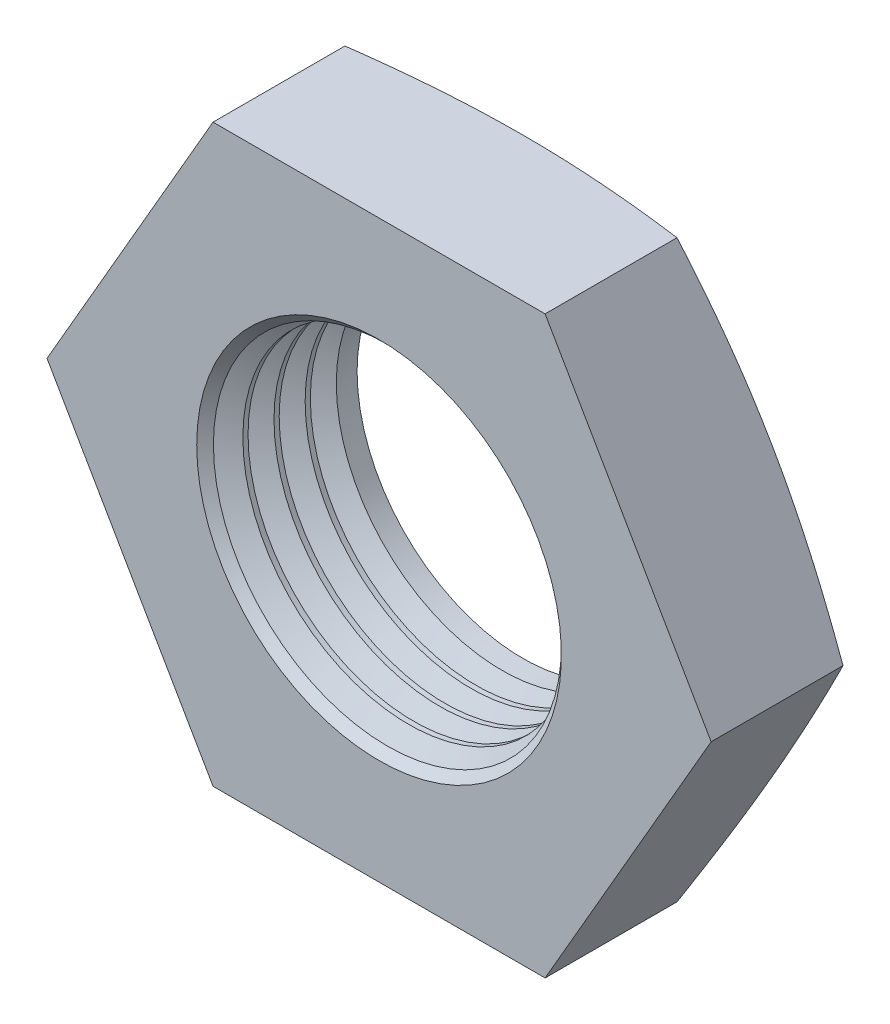
SolidWorks part; units mm, degrees
ref_plane "Front" through (0, 0, 0) normal (0, 0, 1) x (1, 0, 0)
ref_plane "Top" through (0, 0, 0) normal (0, 1, 0) x (1, 0, 0)
ref_plane "Right" through (0, 0, 0) normal (1, 0, 0) x (0, 0, -1)
sketch "Sketch1" plane through (0, 0, 0) normal (0, 0, 1) x (1, 0, 0)
  line L1 (3.4641, -6) -> (6.9282, 0)
  line L2 (6.9282, 0) -> (3.4641, 6)
  line L3 (3.4641, 6) -> (-3.4641, 6)
  line L4 (-3.4641, 6) -> (-6.9282, 0)
  line L5 (-6.9282, 0) -> (-3.4641, -6)
  line L6 (-3.4641, -6) -> (3.4641, -6)
  circle A0 centre (0, 0) radius 6 construction
  circle A1 centre (0, 0) radius 3.4585
  dimension "D" = 6.917
  dimension "s" = 12
  dimension "e" = 13.8564
extrude "BaseNut" add sketch "Sketch1" against normal blind 3
cosmetic thread "ThreadCosmetic1" [suppressed] parameters "D2"=8
sketch "Sketch2" plane through (0, 0, 0) normal (0, 1, 0) x (1, 0, 0)
  line L0 (-6.9282, 3) -> (-6, 3)
  line L2 (-6, 3) -> (-6.9282, 2.7513)
  line L3 (-6.9282, 2.7513) -> (-6.9282, 3)
  line L4 (0, 3.3759) -> (0, -9.8171) construction
  line L6 (-9.7712, 1.5) -> (9.8853, 1.5) construction
  dimension "dw" = 12
  dimension "D2" = 1.5
  dimension "Angle" = 15
revolve "Double-Chamfer" cut sketch "Sketch2" angle 360 about L4
chamfer "Chamfer1" distance 0.3458 angle 45 1 edges at (3.4585, 0, 0)
sketch "Sketch3" plane through (0, 0, 0) normal (0, 1, 0) x (1, 0, 0)
  line L0 (0, 2.7394) -> (0, -0.894) construction
  line L1 (2.917, 0.6166) -> (3.4585, 0.6166)
  line L2 (3.4585, 0.6166) -> (3.9275, 0.3458)
  line L3 (3.9275, 0.3458) -> (3.4585, 0.0751)
  line L4 (3.4585, 0.0751) -> (2.917, 0.0751)
  line L5 (2.917, 0.0751) -> (2.917, 0.6166)
  line L6 (3.4585, 0.3458) -> (-3.4585, 0.3458) construction
  dimension "D1" = 0.5415
  dimension "D2" = 6.917
revolve "Cut-Revolve10" cut sketch "Sketch3" angle 360 about L0
pattern_linear "LPattern10" count 4 spacing 0.6498 along (0, 0, -1) of "Cut-Revolve10"
equation "\"dw@Sketch2\" = \"s@Sketch1\""
equation "\"D2@Sketch2\" = \"m@BaseNut\" / 2"
equation "\"D1@Chamfer1\" = \"D@Sketch1\" / 20"
equation "\"D2@Sketch3\" = \"D@Sketch1\""
equation "\"D1@Sketch3\" = (  \"D2@ThreadCosmetic1\" - \"D@Sketch1\" )  / 2"
equation "\"D3@LPattern10\" = \"D1@Sketch3\" * 1.2"
equation "\"D1@LPattern10\" = (  \"m@BaseNut\"  - \"D1@Chamfer1\")  / \"D3@LPattern10\""
